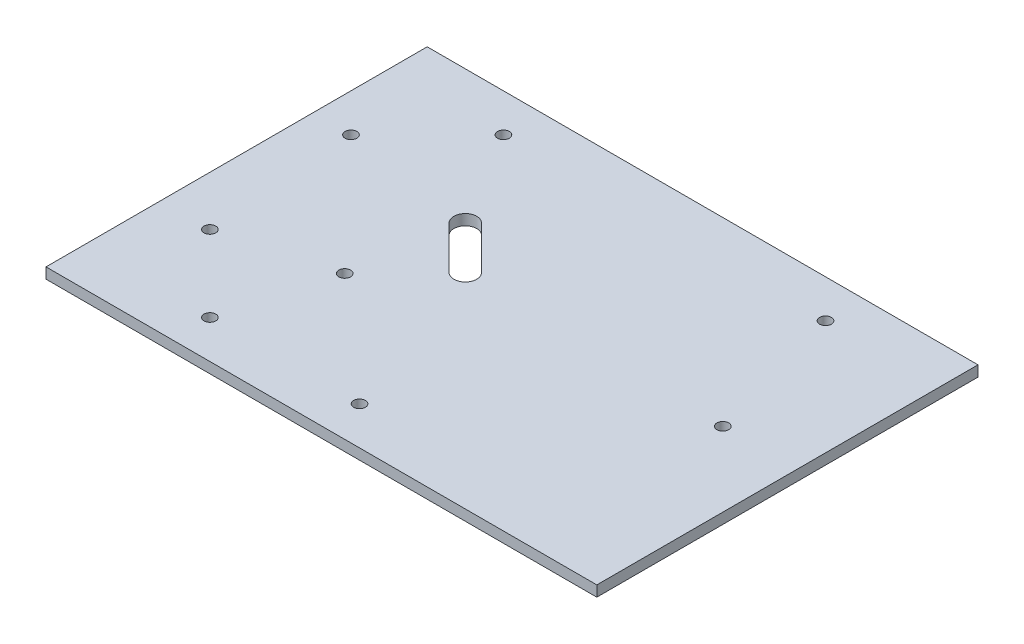
SolidWorks part; units mm, degrees
ref_plane "Front" through (0, 0, 0) normal (0, 0, 1) x (1, 0, 0)
ref_plane "Top" through (0, 0, 0) normal (0, 1, 0) x (1, 0, 0)
ref_plane "Right" through (0, 0, 0) normal (1, 0, 0) x (0, 0, -1)
sketch "Sketch1" plane through (0, 0, 0) normal (0, 1, 0) x (1, 0, 0)
  line L0 (-59.25, -20) -> (-39.25, -40) construction
  line L1 (-72.25, -50) -> (72.25, -50)
  line L2 (-72.25, -50) -> (-72.25, 50)
  line L3 (-72.25, 50) -> (72.25, 50)
  line L4 (72.25, -50) -> (72.25, 50)
  line L5 (-72.25, -50) -> (72.25, 50) construction
  line L6 (-72.25, 50) -> (72.25, -50) construction
  line L7 (-49.25, -30) -> (-31.5723, -12.3223) construction
  circle A0 centre (-59.25, -20) radius 1.55
  circle A1 centre (-39.25, -40) radius 1.55
  circle A2 centre (-31.5723, -12.3223) radius 1.55
  point P0 (0, 0)
  dimension "D3" = 3.1
  dimension "D4" = 3.1
  dimension "D7" = 33
  dimension "D8" = 13
  dimension "D10" = 3.1
  dimension "D1" = 100
  dimension "D2" = 144.5
  dimension "D5" = 30
  dimension "D6" = 10
  dimension "D9" = 25
extrude "Boss-Extrude1" add sketch "Sketch1" along normal blind 2.8
sketch "Sketch2" plane through (0, 2.8, 0) normal (0, 1, 0) x (1, 0, 0)
  line L0 (-27.25, 15) -> (-15.9363, 3.6863) construction
  line L1 (72.25, 50) -> (-72.25, 50) construction
  line L2 (-25.1287, 17.1213) -> (-13.815, 5.8076)
  line L3 (-29.3713, 12.8787) -> (-18.0576, 1.565)
  line L4 (-72.25, 50) -> (-72.25, -50) construction
  arc A1 (-25.1287, 17.1213) -> (-29.3713, 12.8787) centre (-27.25, 15) ccw
  arc A2 (-18.0576, 1.565) -> (-13.815, 5.8076) centre (-15.9363, 3.6863) ccw
  point P4 (-21.5931, 9.3431)
  dimension "D1" = 45
  dimension "D2" = 45
  dimension "D3" = 35
  dimension "D4" = 16
  dimension "D5" = 6
extrude "Cut-Extrude1" cut sketch "Sketch2" against normal up to next
sketch "Sketch3" plane through (0, 2.8, 0) normal (0, 1, 0) x (1, 0, 0)
  line L0 (-72.25, 50) -> (-72.25, -50) construction
  line L1 (72.25, 50) -> (-72.25, 50) construction
  line L2 (72.25, -50) -> (72.25, 50) construction
  line L3 (-72.25, -50) -> (72.25, -50) construction
  circle A0 centre (-62.25, 20) radius 1.55
  circle A1 centre (-42.25, 40) radius 1.55
  circle A2 centre (42.25, 40) radius 1.55
  circle A3 centre (0, -40) radius 1.55
  dimension "D1" = 3.1
  dimension "D2" = 3.1
  dimension "D3" = 3.1
  dimension "D4" = 3.1
  dimension "D5" = 30
  dimension "D6" = 10
  dimension "D7" = 30
  dimension "D8" = 10
  dimension "D9" = 30
  dimension "D10" = 72.25
  dimension "D11" = 10
extrude "Cut-Extrude2" cut sketch "Sketch3" against normal up to next
sketch "Sketch4" plane through (0, 2.8, 0) normal (0, 1, 0) x (1, 0, 0)
  line L0 (72.25, -50) -> (72.25, 50) construction
  line L1 (72.25, 50) -> (-72.25, 50) construction
  circle A0 centre (52.75, 2.56) radius 1.55
  dimension "D1" = 3.1
  dimension "D3" = 47.44
  dimension "D2" = 19.5
extrude "Cut-Extrude3" cut sketch "Sketch4" against normal up to next
